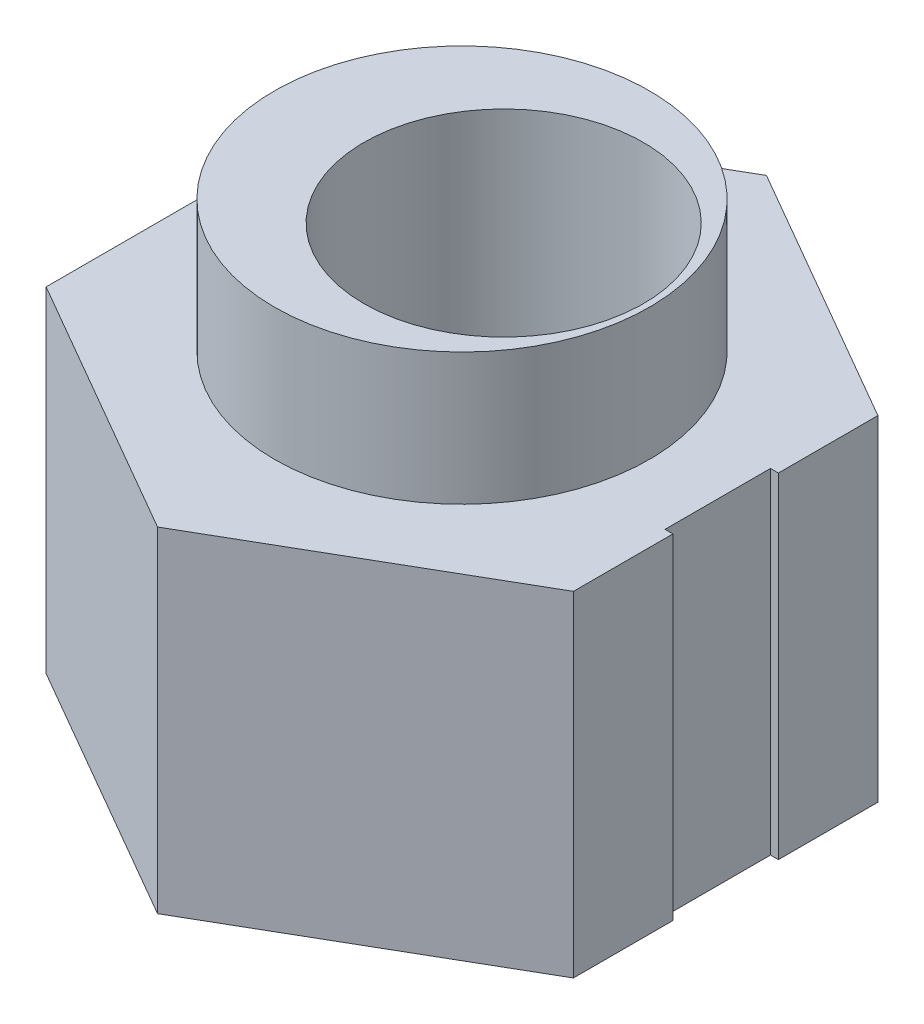
SolidWorks part; units mm, degrees
ref_plane "Front Plane" through (0, 0, 0) normal (0, 0, 1) x (1, 0, 0)
ref_plane "Top Plane" through (0, 0, 0) normal (0, 1, 0) x (1, 0, 0)
ref_plane "Right Plane" through (0, 0, 0) normal (1, 0, 0) x (0, 0, -1)
sketch "Sketch1" plane through (0, 0, 0) normal (0, 1, 0) x (1, 0, 0)
  line L0 (0, 0) -> (-0.79, 0) construction
  line L1 (4.21, 0) -> (0, 0) construction
  line L2 (-0.79, 5.7735) -> (-5.79, 2.8868)
  line L3 (-5.79, 2.8868) -> (-5.79, -2.8868)
  line L4 (-5.79, -2.8868) -> (-0.79, -5.7735)
  line L5 (-0.79, -5.7735) -> (4.21, -2.8868)
  line L6 (4.21, -2.8868) -> (4.21, 2.8868)
  line L7 (4.21, 2.8868) -> (-0.79, 5.7735)
  line L9 (4.06, -1) -> (4.21, -1)
  line L10 (4.06, -1) -> (4.06, 1)
  line L11 (4.06, 1) -> (4.21, 1)
  line L12 (4.21, -1) -> (4.21, 1)
  line L13 (4.06, -1) -> (4.21, 1) construction
  line L14 (4.06, 1) -> (4.21, -1) construction
  circle A0 centre (0, 0) radius 2.65
  circle A1 centre (-0.79, 0) radius 5 construction
  point P12 (4.135, 0)
  dimension "D1" = 5.3
  dimension "D2" = 0.79
  dimension "D3" = 10
  dimension "D4" = 5
  dimension "D5" = 2
  dimension "D6" = 0.15
extrude "Boss-Extrude1" add sketch "Sketch1" along normal blind 6.35 contours L10 L11 L6 L7 L2 L3 L4 L5 L9 A0
sketch "Sketch2" plane through (0, 6.35, 0) normal (0, 1, 0) x (1, 0, 0)
  line L0 (0, 0) -> (-0.79, 0) construction
  circle A0 centre (0, 0) radius 2.65
  circle A1 centre (-0.79, 0) radius 3.555
  dimension "D1" = 5.3
  dimension "D3" = 7.11
  dimension "D2" = 0.79
extrude "Boss-Extrude2" add sketch "Sketch2" along normal blind 2.5
